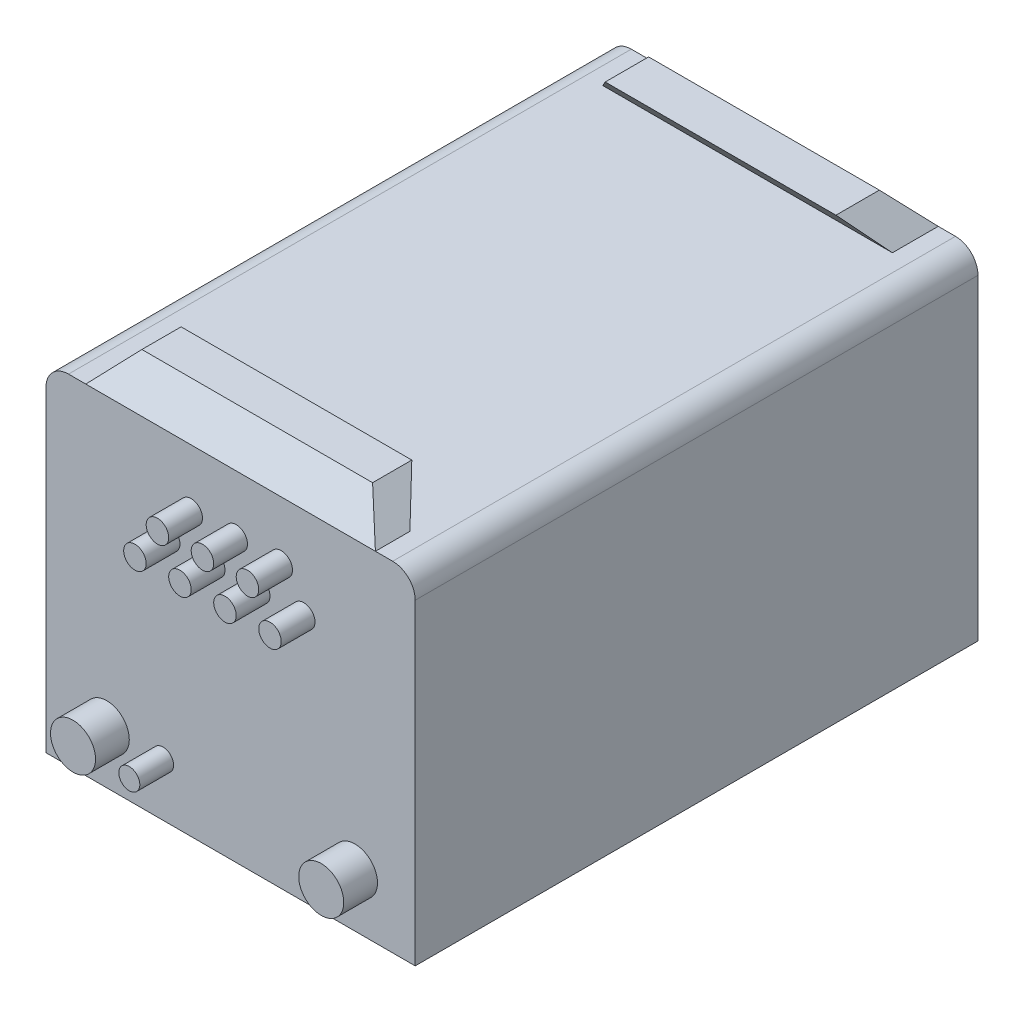
SolidWorks part; units mm, degrees
ref_plane "Спереди" through (0, 0, 0) normal (0, 0, 1) x (1, 0, 0)
ref_plane "Сверху" through (0, 0, 0) normal (0, 1, 0) x (1, 0, 0)
ref_plane "Справа" through (0, 0, 0) normal (1, 0, 0) x (0, 0, -1)
sketch "Эскиз2" plane through (0, 0, 0) normal (0, 0, 1) x (1, 0, 0)
  line L0 (-164, 0) -> (164, 0)
  line L1 (164, 0) -> (164, 281.3464)
  line L2 (144, 301.3464) -> (128.6484, 301.3464)
  line L3 (128.6484, 301.3464) -> (102.4836, 329.1993)
  line L8 (102.4836, 329.1993) -> (-102.4836, 329.1993)
  line L9 (0, 382.3728) -> (0, -59.8962) construction
  line L10 (-144, 301.3464) -> (-128.6484, 301.3464)
  line L11 (-164, 0) -> (-164, 281.3464)
  line L12 (-128.6484, 301.3464) -> (-102.4836, 329.1993)
  arc A0 (-144, 301.3464) -> (-164, 281.3464) centre (-144, 281.3464) ccw
  arc A1 (164, 281.3464) -> (144, 301.3464) centre (144, 281.3464) ccw
  point P9 (0, 0)
  point P13 (0, 329.1993)
  point P15 (-164, 301.3464)
  point P18 (164, 301.3464)
  dimension "D1" = 20
extrude "Бобышка-Вытянуть1" add sketch "Эскиз2" along normal blind 500
sketch "Эскиз3" plane through (0, 0, 0) normal (1, 0, 0) x (0, 0, -1)
  line L0 (-463.1385, 344.7334) -> (-500, 301.3464)
  line L2 (-40.6902, 344.7334) -> (0, 301.3464)
  line L3 (-500, 301.3464) -> (-514.6133, 301.3464)
  line L4 (-514.6133, 301.3464) -> (-514.6133, 363.3709)
  line L5 (-514.6133, 363.3709) -> (0, 363.3709)
  line L6 (0, 301.3464) -> (0, 363.3709)
  line L7 (-469.3509, 301.3464) -> (-431.2388, 339.4586)
  line L8 (-500, 301.3464) -> (0, 301.3464) construction
  line L10 (-73.5276, 339.4586) -> (-40.6902, 301.3464)
  line L11 (-469.3509, 301.3464) -> (-40.6902, 301.3464)
  line L12 (-463.1385, 344.7334) -> (-431.2388, 339.4586)
  line L13 (-73.5276, 339.4586) -> (-40.6902, 344.7334)
extrude "Вырез-Вытянуть1" cut sketch "Эскиз3" against normal mid plane 330
sketch "Эскиз4" plane through (0, 0, 500) normal (0, 0, 1) x (1, 0, 0)
  circle A0 centre (-110, 47.0693) radius 20
  circle A1 centre (-60, 47.0693) radius 9.341
  circle A2 centre (110.5093, 47.0693) radius 20
  circle A3 centre (-35, 250) radius 10
  circle A4 centre (-55, 220) radius 10
  circle A5 centre (-15, 220) radius 10
  circle A6 centre (25, 220) radius 10
  circle A7 centre (65, 220) radius 10
  circle A8 centre (5, 250) radius 10
  circle A9 centre (45, 250) radius 10
  point P18 (0, 0)
  point P21 (0, 0)
  dimension "D1" = 4
  dimension "D2" = 3
sketch "Эскиз5" plane through (0, 0, 0) normal (0, 0, -1) x (-1, 0, 0)
  circle A0 centre (-12.3022, 29.9341) radius 8.2549
  circle A1 centre (-73.8134, 29.9341) radius 9.2267
extrude "Бобышка-Вытянуть2" add sketch "Эскиз4" along normal blind 30
extrude "Бобышка-Вытянуть3" add sketch "Эскиз5" along normal blind 30
